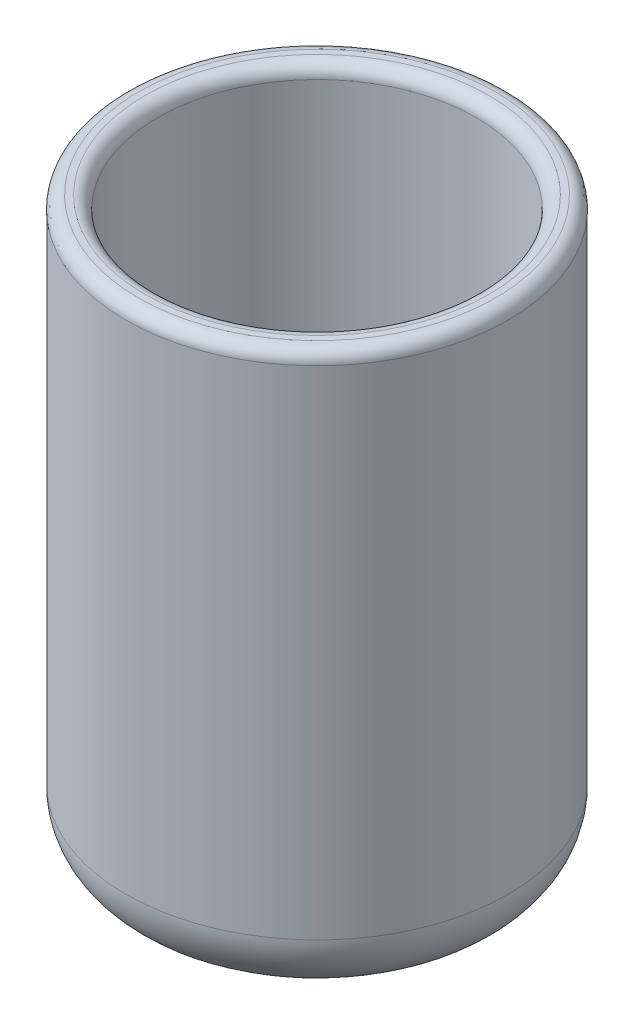
SolidWorks part; units mm, degrees
ref_plane "Alzado" through (0, 0, 0) normal (0, 0, 1) x (1, 0, 0)
ref_plane "Planta" through (0, 0, 0) normal (0, 1, 0) x (1, 0, 0)
ref_plane "Vista lateral" through (0, 0, 0) normal (1, 0, 0) x (0, 0, -1)
sketch "Croquis1" plane through (0, 0, 0) normal (0, 1, 0) x (1, 0, 0)
  circle A0 centre (0, 0) radius 38.1
  dimension "D1" = 76.2
extrude "Saliente-Extruir1" add sketch "Croquis1" along normal blind 114.3
shell "Vaciado5" thickness 10
sketch "Croquis2" plane through (0, 114.3, 0) normal (0, 1, 0) x (1, 0, 0)
  circle A0 centre (0, 0) radius 31.75
  circle A1 centre (0, 0) radius 38.1 construction
  dimension "D1" = 6.35
extrude "Cortar-Extruir1" cut sketch "Croquis2" against normal blind 107.95
fillet "Redondeo1" radius 2.54 2 edges at (0, 114.3, 38.1) (0, 114.3, 31.75)
fillet "Redondeo2" radius 12.7 1 edges at (0, 0, 38.1)
